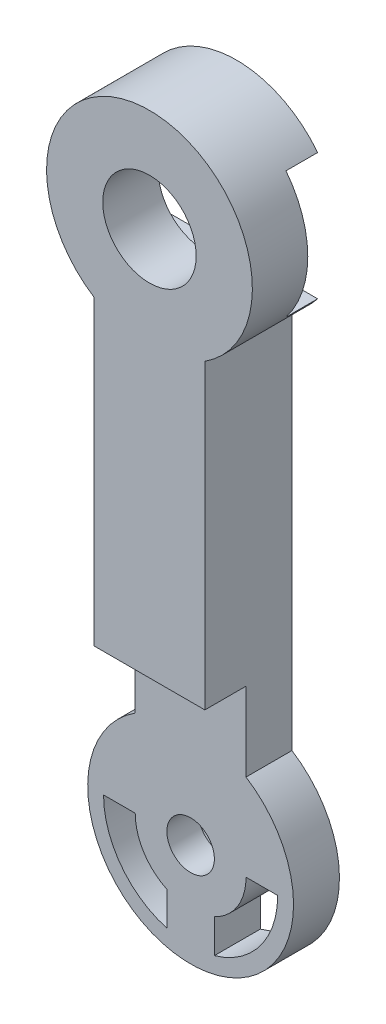
SolidWorks part; units mm, degrees
ref_plane "Front Plane" through (0, 0, 0) normal (0, 0, 1) x (1, 0, 0)
ref_plane "Top Plane" through (0, 0, 0) normal (0, 1, 0) x (1, 0, 0)
ref_plane "Right Plane" through (0, 0, 0) normal (1, 0, 0) x (0, 0, -1)
sketch "Sketch1" plane through (0, 0, 0) normal (0, 0, 1) x (1, 0, 0)
  line L0 (0, 0) -> (0, -35) construction
  line L1 (-3.5, 0) -> (-5.5, 0)
  line L2 (3.5, 0) -> (5.5, 0)
  line L3 (0, -17.5) -> (10.3868, -17.5) construction
  line L5 (-1.5, 3.1623) -> (-1.5, 5.2915)
  line L7 (1.5, 3.1623) -> (1.5, 5.2915)
  line L8 (1.5, -38.1623) -> (1.5, -40.2915)
  line L9 (-1.5, -38.1623) -> (-1.5, -40.2915)
  line L10 (3.5, -35) -> (5.5, -35)
  line L11 (-3.5, -35) -> (-5.5, -35)
  line L13 (-3.5, 0) -> (3.5, 0)
  line L14 (-3.5, 0) -> (-3.5, -35)
  line L15 (-3.5, -35) -> (3.5, -35)
  line L16 (3.5, 0) -> (3.5, -35)
  circle A0 centre (0, 0) radius 2.95
  circle A1 centre (0, 0) radius 6.5
  circle A2 centre (0, 0) radius 3.5
  circle A3 centre (0, 0) radius 5.5
  circle A4 centre (0, -35) radius 5.5
  circle A5 centre (0, -35) radius 3.5
  circle A6 centre (0, -35) radius 6.5
  circle A7 centre (0, -35) radius 2.95
  dimension "D1" = 5.9
  dimension "D2" = 13
  dimension "D3" = 11
  dimension "D4" = 7
  dimension "D5" = 35
extrude "Boss-Extrude1" add sketch "Sketch1" along normal blind 3.7 contours L14 A6 L16 A1 | A3 L16 A1 L14 | L14 A3 L16 A2 | A3 L14 A1 L16 | A6 L14 A4 L16 | A6 L16 A4 L14 | L14 A5 L16 A4 | A4 L11 L14 | A4 L16 L10 | L15 A7 A5 | L15 A7 A5 | L7 A3 L5 A2 | L1 A3 L14 | L16 A3 L2 | L13 A2 A0 | L13 A2 A0 | L8 A5 L9 A4
sketch "Sketch2" plane through (0, 0, 0) normal (1, 0, 0) x (0, 0, -1)
  line L0 (0, 0) -> (0, -24.55) construction
  line L1 (0, -5.4772) -> (0, -29.5228) construction
  line L2 (-3.7, -5.4772) -> (-3.7, -29.5228) construction
  line L3 (-3.7, -24.55) -> (-3.1, -24.55)
  line L4 (-3.7, -24.55) -> (-3.7, -41.5)
  line L5 (-3.7, -41.5) -> (-3.1, -41.5)
  line L6 (-3.1, -24.55) -> (-3.1, -41.5)
  line L7 (-3.7, -41.5) -> (0, -41.5) construction
  dimension "D1" = 24.55
  dimension "D2" = 0.6
extrude "Cut-Extrude1" cut sketch "Sketch2" against normal blind 10 and the other way blind 10
sketch "Sketch3" plane through (0, 0, 0) normal (0, 0, -1) x (-1, 0, 0)
  circle A0 centre (0, -35) radius 2.95
  circle A1 centre (0, -35) radius 1.5
  dimension "D1" = 3
extrude "Boss-Extrude2" add sketch "Sketch3" against normal blind 3.1
sketch "Sketch4" plane through (0, 0, 0) normal (0, 0, -1) x (-1, 0, 0)
  circle A0 centre (0, -35) radius 2.5
  dimension "D1" = 5
extrude "Cut-Extrude2" cut sketch "Sketch4" against normal blind 1.5
sketch "Sketch5" plane through (0, 0, 3.1) normal (0, 0, 1) x (1, 0, 0)
  line L1 (-3.5, -24.55) -> (3.5, -24.55)
  line L2 (-3.5, -24.55) -> (-3.5, -29.5228)
  line L4 (3.5, -24.55) -> (3.5, -29.5228)
  line L5 (-5.5, -35) -> (-3.5, -35)
  line L8 (-1.5, -38.1623) -> (-1.5, -40.2915)
  line L9 (5.5, -35) -> (3.5, -35)
  line L12 (1.5, -38.1623) -> (1.5, -40.2915)
  circle A0 centre (0, -35) radius 1.5
  circle A1 centre (0, -35) radius 6.5
  circle A2 centre (0, -35) radius 3.5
  arc A3 (-5.5, -35) -> (5.5, -35) centre (0, -35) ccw
extrude "Boss-Extrude3" add sketch "Sketch5" along normal blind 0.4
sketch "Sketch6" plane through (0, 0, 3.7) normal (0, 0, 1) x (1, 0, 0)
  line L0 (-1.5, 5.2915) -> (-1.5, 3.1623)
  line L2 (-3.5, -5.4772) -> (-3.5, -24.55)
  line L3 (-3.5, -24.55) -> (3.5, -24.55)
  line L4 (3.5, -5.4772) -> (3.5, -24.55)
  line L5 (1.5, 5.2915) -> (1.5, 3.1623)
  line L6 (3.5, 0) -> (5.5, 0)
  line L7 (-5.5, 0) -> (-3.5, 0)
  circle A0 centre (0, 0) radius 2.95
  arc A1 (3.5, -5.4772) -> (-3.5, -5.4772) centre (0, 0) ccw
  arc A2 (-1.5, 5.2915) -> (-5.5, 0) centre (0, 0) ccw
  arc A3 (-1.5, 3.1623) -> (-3.5, 0) centre (0, 0) ccw
  arc A4 (3.5, 0) -> (1.5, 3.1623) centre (0, 0) ccw
  arc A5 (5.5, 0) -> (1.5, 5.2915) centre (0, 0) ccw
extrude "Boss-Extrude4" add sketch "Sketch6" along normal blind 2.4
sketch "Sketch7" plane through (0, 0, 0) normal (0, 0, 1) x (1, 0, 0)
  line L1 (12.005, 7.8195) -> (-10.0995, 7.8195)
  line L2 (12.005, 7.8195) -> (12.005, -42.7273)
  line L3 (12.005, -42.7273) -> (-10.0995, -42.7273)
  line L4 (-10.0995, 7.8195) -> (-10.0995, -42.7273)
extrude "Cut-Extrude3" cut sketch "Sketch7" along normal blind 0.6
sketch "Sketch8" plane through (0, 0, 6.1) normal (0, 0, 1) x (1, 0, 0)
  circle A0 centre (0, 0) radius 5.5
  circle A1 centre (0, 0) radius 3.5
extrude "Boss-Extrude5" add sketch "Sketch8" against normal blind 5.5
sketch "Sketch9" plane through (0, 0, 0.6) normal (0, 0, -1) x (-1, 0, 0)
  line L0 (-8.8322, 4) -> (-8.8322, -4)
  line L1 (-8.8322, 4) -> (8.8322, 4)
  line L2 (0, 4) -> (0, -4)
  line L3 (-8.8322, -4) -> (8.8322, -4)
  line L4 (8.8322, 4) -> (8.8322, -4)
  circle A0 centre (0, 0) radius 2.95 construction
  arc A1 (3.5, -5.4772) -> (-3.5, -5.4772) centre (0, 0) ccw construction
  arc M13 (3.5, -5.4772) -> (-3.5, -5.4772) centre (0, 0) ccw
  circle M16 centre (0, 0) radius 2.95
  dimension "D1" = 4
  dimension "D2" = 4
extrude "Cut-Extrude4" cut sketch "Sketch9" against normal blind 2 contours L3 L2 L1 M13 M16 | L2 L3 L1 M13 M16
